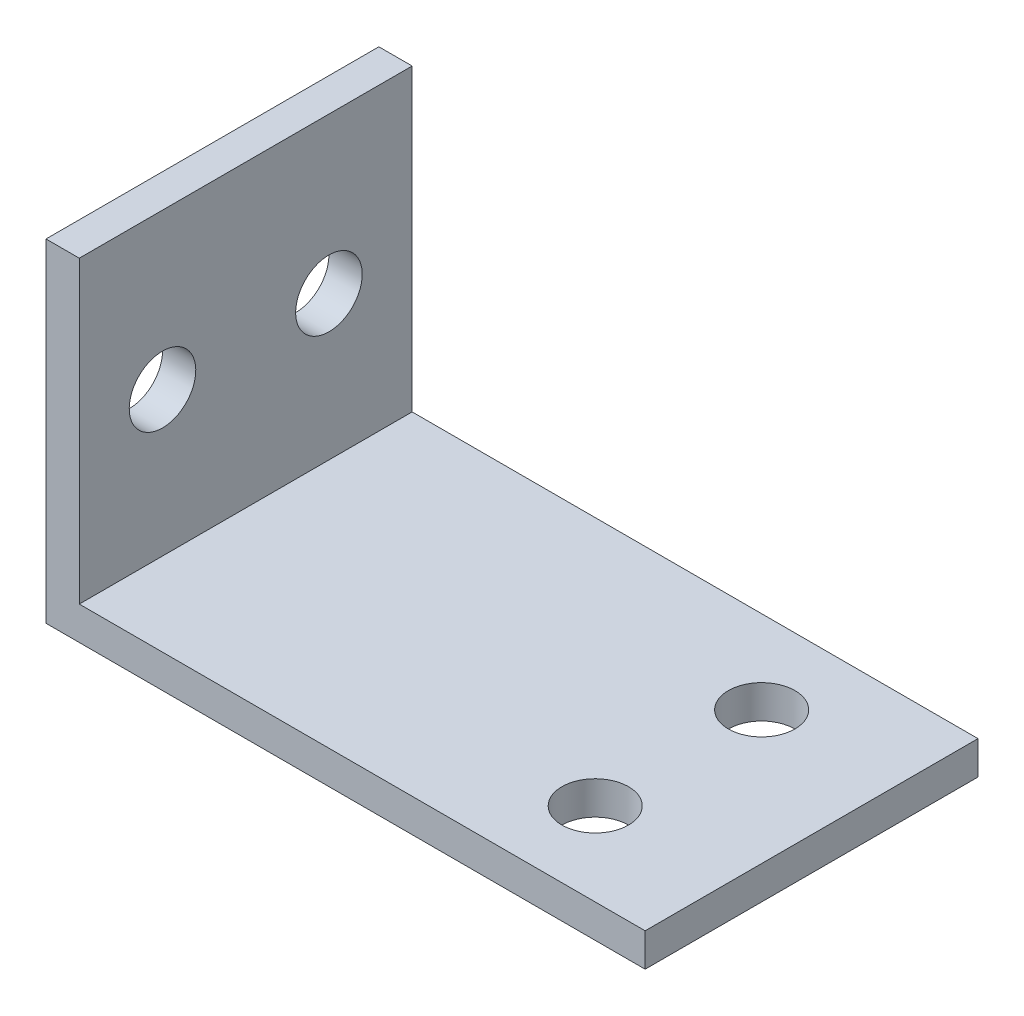
SolidWorks part; units mm, degrees
ref_plane "Ebene vorne" through (0, 0, 0) normal (0, 0, 1) x (1, 0, 0)
ref_plane "Ebene oben" through (0, 0, 0) normal (0, 1, 0) x (1, 0, 0)
ref_plane "Ebene rechts" through (0, 0, 0) normal (1, 0, 0) x (0, 0, -1)
sketch "Skizze1" plane through (0, 0, 0) normal (0, 0, 1) x (1, 0, 0)
  line L0 (-11, 21) -> (-11, 51)
  line L2 (-11, 51) -> (-14, 51)
  line L3 (-14, 51) -> (-14, 24)
  line L4 (-14, 24) -> (-35, 24)
  line L5 (-35, 24) -> (-35, 21)
  line L6 (-35, 21) -> (-11, 21)
  line L8 (65, 21) -> (11, 21)
  line L9 (65, 24) -> (65, 21)
  line L10 (14, 24) -> (65, 24)
  line L11 (14, 51) -> (14, 24)
  line L12 (11, 51) -> (14, 51)
  line L13 (11, 21) -> (11, 51)
sketch "Skizze2" plane through (0, 0, 0) normal (0, 0, 1) x (1, 0, 0)
  line L32 (14, 51) -> (11, 51)
  line L33 (14, 24) -> (14, 51)
  line L34 (65, 24) -> (14, 24)
  line L35 (65, 21) -> (65, 24)
  line L36 (11, 21) -> (65, 21)
  line L37 (11, 51) -> (11, 21)
  line L38 (14, 51) -> (11, 51)
  line L39 (14, 24) -> (14, 51)
  line L40 (65, 24) -> (14, 24)
  line L41 (65, 21) -> (65, 24)
  line L42 (11, 21) -> (65, 21)
  line L43 (11, 51) -> (11, 21)
  dimension "D1" = 0
sketch "Skizze3" plane through (0, 0, 0) normal (0, 1, 0) x (0, 0, -1)
  line L0 (15, 0) -> (-15, 0)
  point P8 (0, 0)
extrude "Aufsatz-Linear austragen1" add sketch "Skizze2" along normal up to vertex (15 mm away) and the other way up to vertex (15 mm away) up to point (0, 0, 15) other way up to point (0, 0, -15)
sketch "Skizze4" plane through (0, 0, 0) normal (0, 1, 0) x (1, 0, 0)
  line L1 (0, 0) -> (30.9843, 0) construction
  line L4 (-65, -15) -> (65, -15)
  line L5 (-65, -15) -> (-65, 15)
  line L6 (-65, 15) -> (65, 15)
  line L7 (65, -15) -> (65, 15)
  line L8 (-65, -15) -> (65, 15) construction
  line L9 (-65, 15) -> (65, -15) construction
  circle A0 centre (53, -7.5) radius 1.65
  circle A1 centre (53, 7.5) radius 1.65
  circle A2 centre (-53, 7.5) radius 1.65
  circle A3 centre (-53, -7.5) radius 1.65
  point P8 (0, 0)
sketch "Skizze5" plane through (0, 0, 0) normal (0, 1, 0) x (1, 0, 0)
  circle A0 centre (53, -7.5) radius 3
  circle A1 centre (53, 7.5) radius 3
  dimension "D1" = 6
  dimension "D2" = 6
extrude "Schnitt-Linear austragen1" cut sketch "Skizze5" along normal up to surface (24 mm away) up to face at (39.5, 24, 0)
sketch "Skizze6" plane through (0, 0, 0) normal (1, 0, 0) x (0, 0, -1)
  line L2 (0, 90) -> (21.451, 90) construction
  circle A0 centre (7.5, 37) radius 3
  circle A1 centre (-7.5, 37) radius 3
  circle A4 centre (-7.5, 143) radius 3
  circle A5 centre (7.5, 143) radius 3
sketch "Skizze7" plane through (0, 0, 0) normal (1, 0, 0) x (0, 0, -1)
  circle A5 centre (7.5, 37) radius 3
  circle A6 centre (-7.5, 37) radius 3
  dimension "D1" = 6
  dimension "D2" = 6
extrude "Schnitt-Linear austragen2" cut sketch "Skizze7" along normal up to surface (14 mm away) up to face at (14, 37.5, 0)
